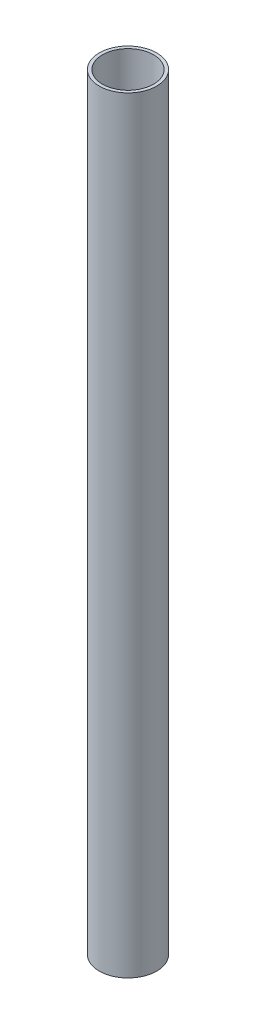
SolidWorks part; units mm, degrees
material "ASTM A36 Steel"
ref_plane "Front Plane" through (0, 0, 0) normal (0, 0, 1) x (1, 0, 0)
ref_plane "Top Plane" through (0, 0, 0) normal (0, 1, 0) x (1, 0, 0)
ref_plane "Right Plane" through (0, 0, 0) normal (1, 0, 0) x (0, 0, -1)
sketch "Sketch1" plane through (0, 0, 0) normal (0, 1, 0) x (1, 0, 0)
  circle A0 centre (0, 0) radius 57.15
  circle A1 centre (0, 0) radius 50.8
  dimension "D1" = 114.3
  dimension "D2" = 101.6
extrude "Boss-Extrude1" add sketch "Sketch1" along normal blind 1524
